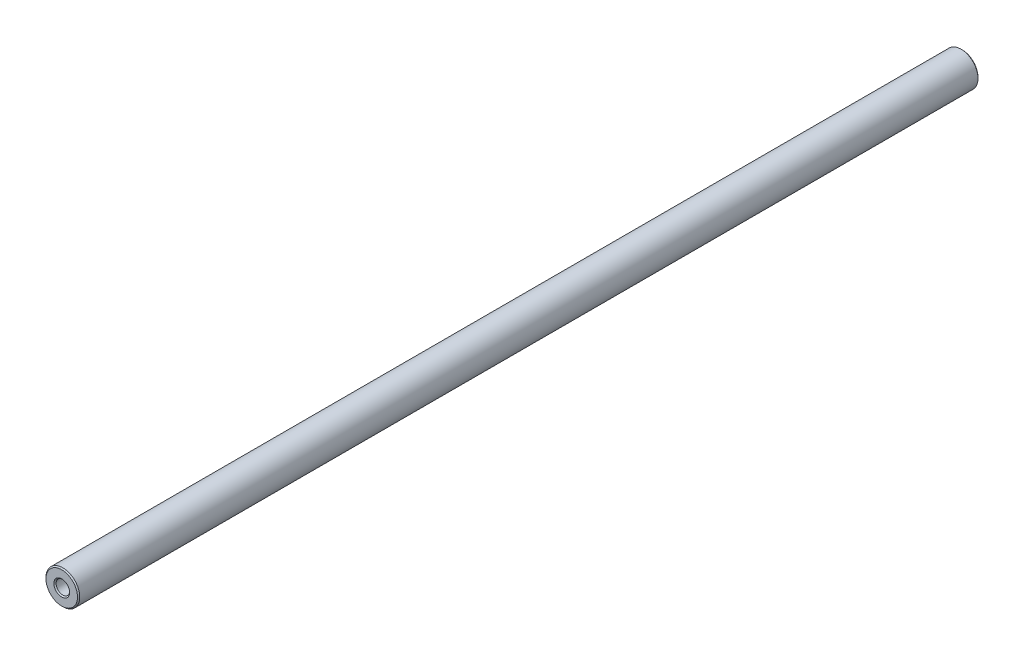
SolidWorks part; units mm, degrees
ref_plane "前视基准面" through (0, 0, 0) normal (0, 0, 1) x (1, 0, 0)
ref_plane "上视基准面" through (0, 0, 0) normal (0, 1, 0) x (1, 0, 0)
ref_plane "右视基准面" through (0, 0, 0) normal (1, 0, 0) x (0, 0, -1)
sketch "Sketch1" plane through (0, 0, 0) normal (0, 0, 1) x (1, 0, 0)
  circle A0 centre (0, 0) radius 3
  dimension "D1" = 6
extrude "Boss-Extrude1" add sketch "Sketch1" along normal blind 160
sketch "Sketch2" plane through (0, 0, 160) normal (0, 0, 1) x (1, 0, 0)
  circle A0 centre (0, 0) radius 1.2
  dimension "D1" = 2.4
extrude "Cut-Extrude1" cut sketch "Sketch2" against normal blind 12
cosmetic thread "Cosmetic Thread1"
sketch "Sketch3" plane through (0, 0, 0) normal (0, 0, -1) x (-1, 0, 0)
  circle A0 centre (0, 0) radius 1.2
  dimension "D1" = 2.4
extrude "Cut-Extrude2" cut sketch "Sketch3" against normal blind 12
cosmetic thread "Cosmetic Thread2"
chamfer "Chamfer1" distance 0.2 angle 45 4 edges at (3, 0, 160) (1.2, 0, 160) (3, 0, 0) (-1.2, 0, 0)
